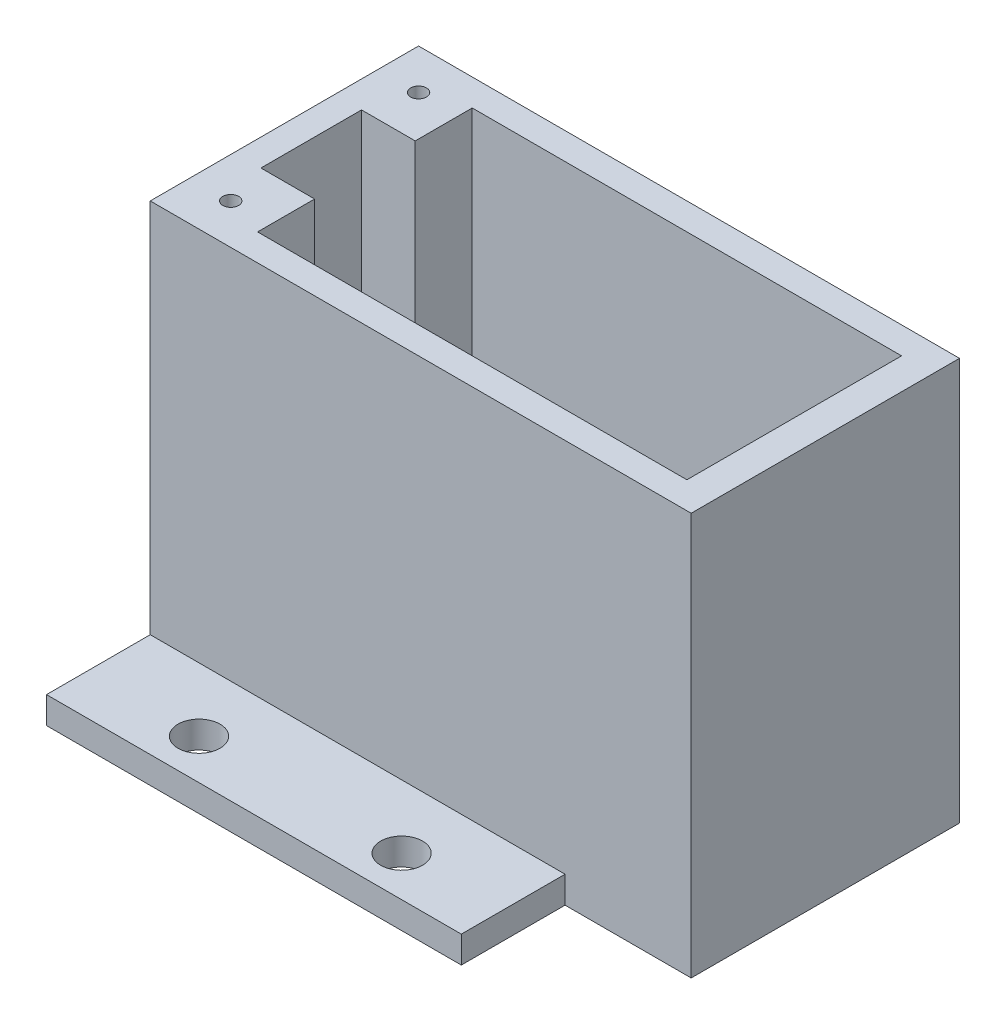
SolidWorks part; units mm, degrees
ref_plane "Front Plane" through (0, 0, 0) normal (0, 0, 1) x (1, 0, 0)
ref_plane "Top Plane" through (0, 0, 0) normal (0, 1, 0) x (1, 0, 0)
ref_plane "Right Plane" through (0, 0, 0) normal (1, 0, 0) x (0, 0, -1)
sketch "Sketch1" plane through (0, 0, 0) normal (0, 1, 0) x (1, 0, 0)
  line L1 (45.593, -45) -> (-45.593, -45)
  line L2 (45.593, -45) -> (45.593, 45)
  line L3 (45.593, 45) -> (-45.593, 45)
  line L4 (-45.593, -45) -> (-45.593, 45)
  circle A0 centre (26.67, -37.38) radius 3.9688
  circle A1 centre (-11.684, -37.38) radius 3.9688
  circle A2 centre (-11.684, 37.38) radius 3.9688
  circle A3 centre (26.67, 37.38) radius 3.9688
  point P0 (0, 0)
  dimension "D3" = 7.9375
  dimension "D1" = 91.186
  dimension "D2" = 90
  dimension "D4" = 18.923
  dimension "D5" = 57.277
  dimension "D6" = 7.62
  dimension "D7" = 7.62
extrude "Mounting plate extrude" add sketch "Sketch1" along normal blind 5.08
sketch "Sketch3" plane through (0, 5.08, 0) normal (0, 1, 0) x (1, 0, 0)
  line L0 (45.593, -45) -> (45.593, 45) construction
  line L1 (69.469, -25.358) -> (-32.941, -25.358)
  line L2 (69.469, -25.358) -> (69.469, 25.442)
  line L3 (69.469, 25.442) -> (-32.941, 25.442)
  line L4 (-32.941, -25.358) -> (-32.941, 25.442)
  line L6 (45.593, 45) -> (-45.593, 45) construction
  line L12 (-17.701, 9.567) -> (-17.701, 20.362)
  line L13 (-17.701, 20.362) -> (63.579, 20.362)
  line L14 (63.579, 9.567) -> (63.579, 20.362)
  line L15 (-17.701, -9.483) -> (-27.861, -9.483)
  line L16 (63.579, -9.483) -> (63.579, 9.567)
  line L17 (-17.701, 9.567) -> (-27.861, 9.567)
  line L18 (-27.861, -9.483) -> (-27.861, 9.567)
  line L20 (-17.701, -9.483) -> (-17.701, -20.278)
  line L21 (-17.701, -20.278) -> (63.579, -20.278)
  line L22 (63.579, -9.483) -> (63.579, -20.278)
  point P0 (0, 0)
  point P6 (0, 0)
  point P7 (0, 0)
  dimension "D1" = 102.41
  dimension "D2" = 50.8
  dimension "D3" = 91.44
  dimension "D4" = 23.876
  dimension "D5" = 19.558
  dimension "D6" = 19.05
  dimension "D7" = 5.08
  dimension "D8" = 15.875
  dimension "D9" = 5.08
  dimension "D10" = 5.08
  dimension "D11" = 15.24
  dimension "D12" = 15.24
extrude "Main extrude" add sketch "Sketch3" along normal blind 71.12
sketch "Sketch4" plane through (0, 5.08, 0) normal (0, -1, 0) x (1, 0, 0)
  line L1 (69.469, -25.442) -> (45.593, -25.442)
  line L2 (69.469, -25.442) -> (69.469, 25.358)
  line L3 (69.469, 25.358) -> (45.593, 25.358)
  line L4 (45.593, -25.442) -> (45.593, 25.358)
extrude "Boss-Extrude3" add sketch "Sketch4" along normal blind 5.08
sketch "Sketch5" plane through (0, 76.2, 0) normal (0, 1, 0) x (1, 0, 0)
  line L0 (45.593, 25.442) -> (-32.941, 25.442) construction
  line L1 (-32.941, 25.442) -> (-32.941, -25.358) construction
  line L2 (-32.941, 25.442) -> (-32.941, -25.358) construction
  line L3 (-32.941, -25.358) -> (69.469, -25.358) construction
  circle A0 centre (-25.321, 17.822) radius 1.5
  circle A1 centre (-25.321, -17.738) radius 1.5
  dimension "D1" = 3
  dimension "D4" = 7.62
  dimension "D5" = 7.62
  dimension "D2" = 7.62
  dimension "D3" = 7.62
extrude "Cut-Extrude1" cut sketch "Sketch5" against normal blind 25.4
sketch "Sketch7" plane through (0, 5.08, 0) normal (0, 1, 0) x (1, 0, 0)
  line L0 (45.593, 45) -> (-45.593, 45) construction
  line L1 (-45.593, -45) -> (-32.941, -45)
  line L2 (-45.593, -45) -> (-45.593, 45)
  line L3 (-45.593, 45) -> (-32.941, 45)
  line L4 (-32.941, -45) -> (-32.941, 45)
  line L5 (-32.941, 25.442) -> (-32.941, -25.358) construction
  dimension "D1" = 0
extrude "Cut-Extrude3" cut sketch "Sketch7" against normal blind 5.08
sketch "Sketch8" plane through (0, 5.08, 0) normal (0, 1, 0) x (1, 0, 0)
  line L0 (-17.701, 20.362) -> (-17.701, 9.567)
  line L1 (-17.701, 9.567) -> (-27.861, 9.567)
  line L2 (-27.861, 9.567) -> (-27.861, -9.483)
  line L3 (-27.861, -9.483) -> (-17.701, -9.483)
  line L4 (-17.701, -9.483) -> (-17.701, -20.278)
  line L5 (-17.701, -20.278) -> (63.579, -20.278)
  line L6 (63.579, -20.278) -> (63.579, 20.362)
  line L7 (63.579, 20.362) -> (-17.701, 20.362)
extrude "Cut-Extrude4" cut sketch "Sketch8" against normal blind 5.08
